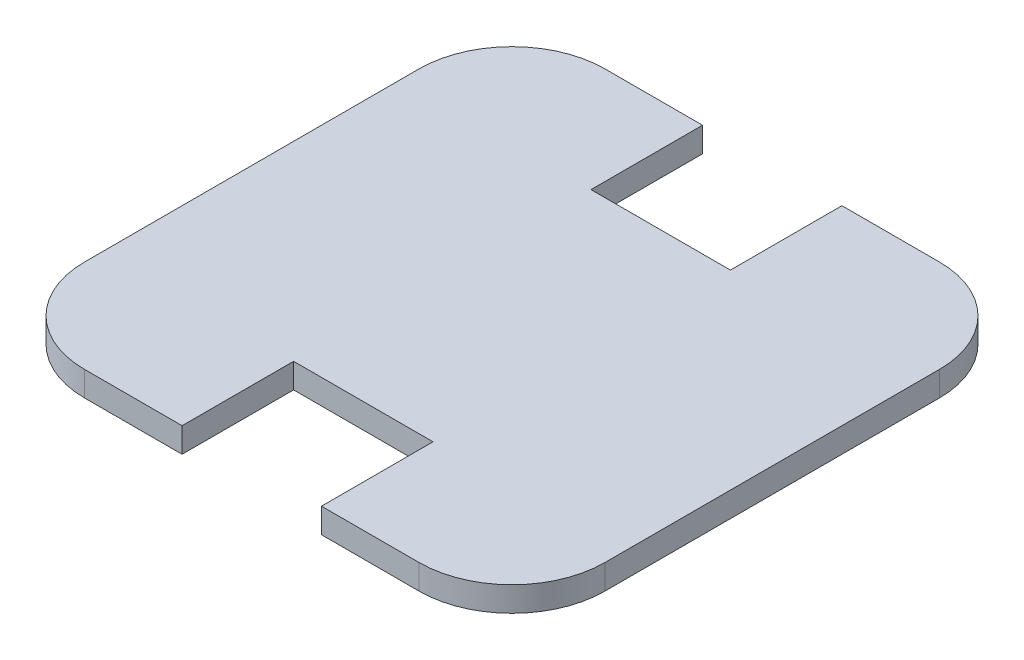
SolidWorks part; units mm, degrees
ref_plane "Front Plane" through (0, 0, 0) normal (0, 0, 1) x (1, 0, 0)
ref_plane "Top Plane" through (0, 0, 0) normal (0, 1, 0) x (1, 0, 0)
ref_plane "Right Plane" through (0, 0, 0) normal (1, 0, 0) x (0, 0, -1)
sketch "Layer1" plane through (0, 0, 0) normal (0, 1, 0) x (1, 0, 0)
  line L0 (11.25, 42) -> (27, 42)
  line L1 (-27, -42) -> (-11.25, -42)
  line L2 (-42, -27) -> (-42, 27)
  line L3 (-27, 42) -> (-11.25, 42)
  line L4 (42, -27) -> (42, 27)
  line L5 (-42, -42) -> (42, 42) construction
  line L6 (-42, 42) -> (42, -42) construction
  line L8 (-11.25, 42) -> (-11.25, 24)
  line L9 (-11.25, 24) -> (11.25, 24)
  line L10 (11.25, 42) -> (11.25, 24)
  line L12 (-11.25, -42) -> (-11.25, -24)
  line L13 (-11.25, -24) -> (11.25, -24)
  line L14 (11.25, -42) -> (11.25, -24)
  line L15 (11.25, -42) -> (27, -42)
  line L18 (-42, -21.5) -> (-42, 21.5)
  arc A0 (27, -42) -> (42, -27) centre (27, -27) ccw
  arc A1 (27, 42) -> (42, 27) centre (27, 27) cw
  arc A2 (-27, -42) -> (-42, -27) centre (-27, -27) cw
  arc A3 (-42, 27) -> (-27, 42) centre (-27, 27) cw
  point P0 (0, 0)
  point P30 (21.7219, 0)
  dimension "D9" = 15
  dimension "D1" = 84
  dimension "D2" = 84
  dimension "D3" = 18
  dimension "D4" = 22.5
  dimension "D5" = 18
  dimension "D6" = 22.5
  dimension "D7" = 30.75
  dimension "D8" = 30.75
  dimension "D10" = 43
extrude "Boss-Extrude1" add sketch "Layer1" along normal blind 4
sketch "Sketch4" plane through (0, 4, 0) normal (0, 1, 0) x (1, 0, 0)
  line L0 (11.25, 42) -> (27, 42) construction
  line L1 (20.125, -26.5) -> (33.125, -26.5)
  line L2 (20.125, -26.5) -> (20.125, 26.5)
  line L3 (20.125, 26.5) -> (33.125, 26.5)
  line L4 (33.125, -26.5) -> (33.125, 26.5)
  line L5 (20.125, -26.5) -> (33.125, 26.5) construction
  line L6 (20.125, 26.5) -> (33.125, -26.5) construction
  line L7 (42, -27) -> (42, 27) construction
  line L8 (-42, -27) -> (-42, 27) construction
  line L9 (-42, 21.5) -> (1, 21.5)
  line L10 (-42, 21.5) -> (-42, -21.5)
  line L11 (-42, -21.5) -> (1, -21.5)
  line L12 (1, 21.5) -> (1, -21.5)
  line L13 (-27, 42) -> (-11.25, 42) construction
  circle A0 centre (-32, 32) radius 5
  circle A1 centre (32, 32) radius 5
  circle A2 centre (32, -32) radius 5
  circle A3 centre (-32, -32) radius 5
  point P0 (26.625, 0)
  dimension "D9" = 10
  dimension "D1" = 53
  dimension "D2" = 13
  dimension "D3" = 15.5
  dimension "D4" = 8.875
  dimension "D5" = 43
  dimension "D6" = 43
  dimension "D7" = 0
  dimension "D8" = 20.5
  dimension "D10" = 10
  dimension "D11" = 10
  dimension "D12" = 2
  dimension "D13" = 2
equation "\"D6@Layer1\"=\"D4@Layer1\""
equation "\"D5@Layer1\"=\"D3@Layer1\""
equation "\"D2@Layer1\"=\"D1@Layer1\""
equation "\"D7@Layer1\"=(\"D2@Layer1\"-\"D4@Layer1\")/2"
equation "\"D8@Layer1\"=\"D7@Layer1\""
equation "\"D3@Sketch4\"=(\"D1@Layer1\"-\"D1@Sketch4\")/2"
equation "\"D4@Sketch4\"=(\"D7@Layer1\"-\"D2@Sketch4\")/2"
equation "\"D6@Sketch4\"=\"D5@Sketch4\""
equation "\"D8@Sketch4\"=(\"D1@Layer1\"-\"D5@Sketch4\")/2"
equation "\"D11@Sketch4\"=\"D10@Sketch4\""
